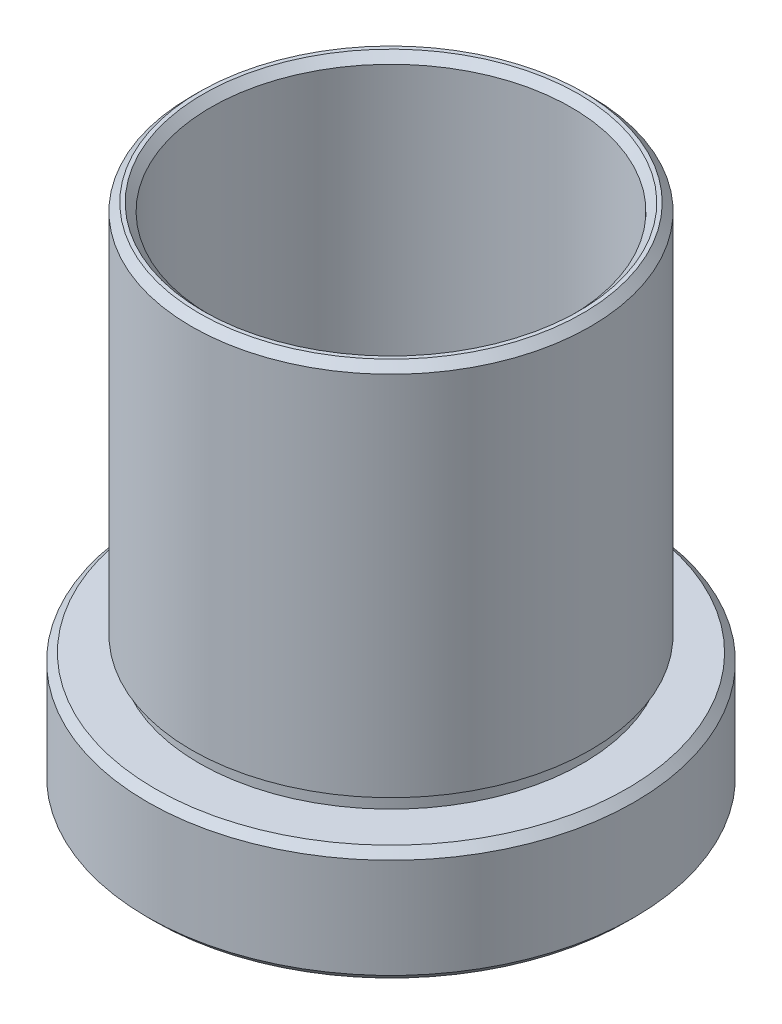
SolidWorks part; units mm, degrees
ref_plane "前视基准面" through (0, 0, 0) normal (0, 0, 1) x (1, 0, 0)
ref_plane "上视基准面" through (0, 0, 0) normal (0, 1, 0) x (1, 0, 0)
ref_plane "右视基准面" through (0, 0, 0) normal (1, 0, 0) x (0, 0, -1)
sketch "草图1" plane through (0, 0, 0) normal (0, 0, 1) x (1, 0, 0)
  line L0 (0, 44.5986) -> (0, -38.4055) construction
  line L1 (12.25, 27.0429) -> (12.5, 27.0429)
  line L2 (13, 26.5429) -> (13, 2.6429)
  line L3 (13, 2.6429) -> (12.5, 2.6429)
  line L4 (12.5, 2.6429) -> (12.5, 1.6429)
  line L5 (12.5, 1.6429) -> (15.375, 1.6429)
  line L6 (15.875, 1.1429) -> (15.875, -5.3571)
  line L7 (15.375, -5.8571) -> (14.75, -5.8571)
  line L8 (14.25, -5.3571) -> (14.25, -1.3571)
  line L9 (14.25, -1.3571) -> (14.35, -1.3571)
  line L10 (14.35, -1.3571) -> (14.35, -0.3571)
  line L11 (15.875, -5.3571) -> (15.375, -5.8571)
  line L12 (11.75, -0.3571) -> (11.75, 26.5429)
  line L13 (14.35, -0.3571) -> (11.75, -0.3571)
  line L14 (14.75, -5.8571) -> (14.25, -5.3571)
  line L15 (12.5, 27.0429) -> (13, 26.5429)
  line L16 (11.75, 26.5429) -> (12.25, 27.0429)
  line L17 (15.375, 1.6429) -> (15.875, 1.1429)
  point P3 (11.75, 27.0429)
  point P4 (13, 27.0429)
  point P9 (15.875, -5.8571)
  point P10 (15.875, 1.6429)
  point P11 (14.25, -5.8571)
  point P13 (12.5, 2.1429)
  point P14 (14.35, -0.8571)
  dimension "D2" = 15.875
  dimension "D3" = 14.25
  dimension "D4" = 13
  dimension "D5" = 11.75
  dimension "D6" = 7.5
  dimension "D7" = 5.5
  dimension "D8" = 1
  dimension "D9" = 1
  dimension "D10" = 12.5
  dimension "D11" = 14.35
revolve "旋转2" add sketch "草图1" angle 360 about L0
